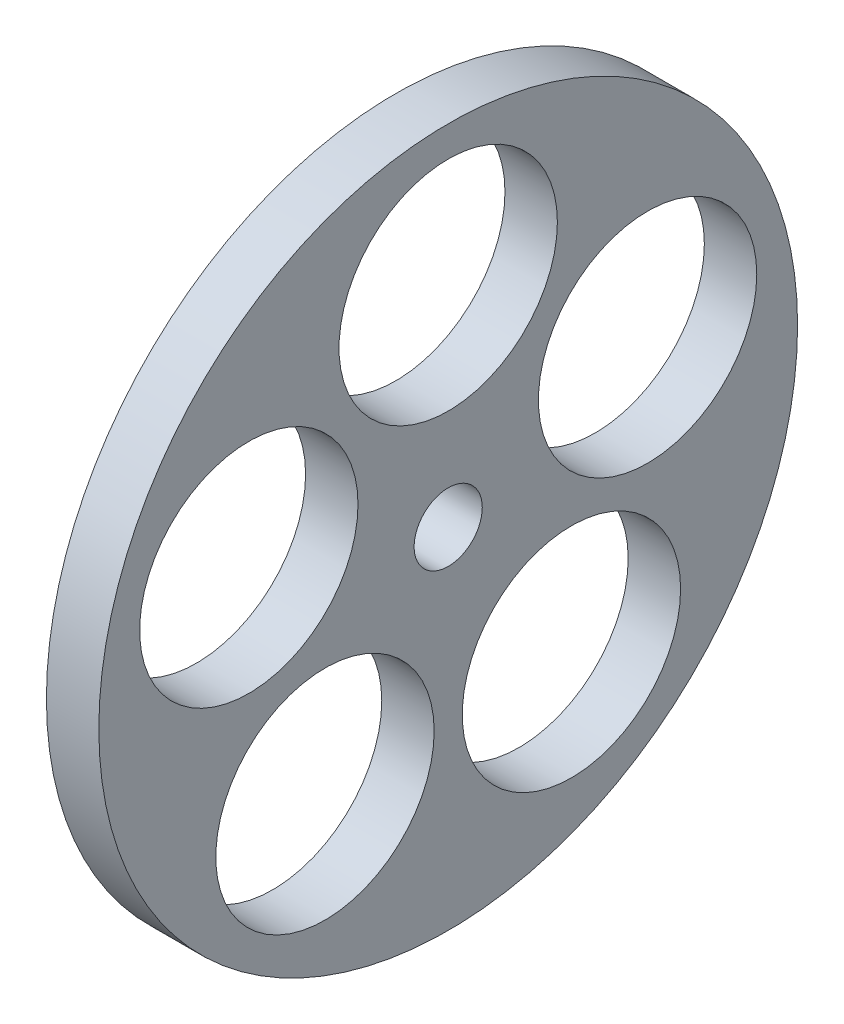
SolidWorks part; units mm, degrees
material "Acrylic (Medium-high impact)"
ref_plane "Front Plane" through (0, 0, 0) normal (0, 0, 1) x (1, 0, 0)
ref_plane "Top Plane" through (0, 0, 0) normal (0, 1, 0) x (1, 0, 0)
ref_plane "Right Plane" through (0, 0, 0) normal (1, 0, 0) x (0, 0, -1)
sketch "Sketch1" plane through (0, 0, 0) normal (1, 0, 0) x (0, 0, -1)
  line L0 (0, 3.9) -> (0, 40) construction
  circle A0 centre (0, 0) radius 40
  circle A1 centre (0, 0) radius 3.9
  circle A2 centre (0, 24) radius 12.5
  circle A3 centre (22.8254, 7.4164) radius 12.5
  circle A4 centre (14.1068, -19.4164) radius 12.5
  circle A5 centre (-14.1068, -19.4164) radius 12.5
  circle A6 centre (-22.8254, 7.4164) radius 12.5
  point P18 (0, 0)
  dimension "D1" = 80
  dimension "D2" = 7.8
  dimension "D3" = 25
  dimension "D5" = 24
  dimension "D4" = 5
extrude "Boss-Extrude1" add sketch "Sketch1" along normal blind 6
